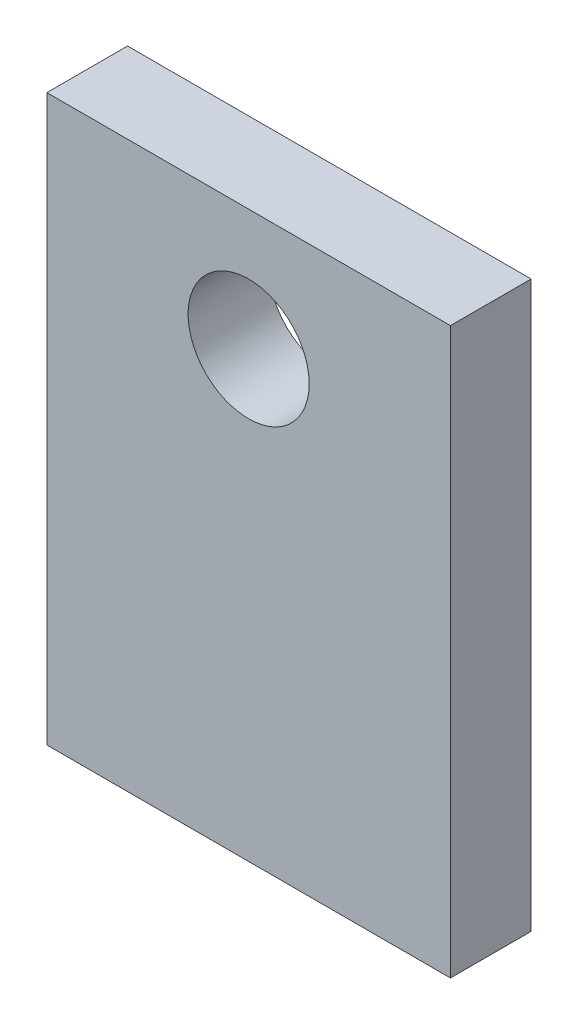
SolidWorks part; units mm, degrees
ref_plane "Front" through (0, 0, 0) normal (0, 0, 1) x (1, 0, 0)
ref_plane "Top" through (0, 0, 0) normal (0, 1, 0) x (1, 0, 0)
ref_plane "Right" through (0, 0, 0) normal (1, 0, 0) x (0, 0, -1)
sketch "Sketch1" plane through (0, 0, 0) normal (0, 0, 1) x (1, 0, 0)
  line L1 (0, 0) -> (127, 0)
  line L2 (0, 0) -> (0, 177.8)
  line L3 (0, 177.8) -> (127, 177.8)
  line L4 (127, 0) -> (127, 177.8)
  circle A0 centre (63.5, 139.7) radius 19.05
  dimension "D3" = 38.1
  dimension "D1" = 127
  dimension "D2" = 177.8
  dimension "D4" = 63.5
extrude "Base-Extrude" add sketch "Sketch1" along normal blind 25.4
